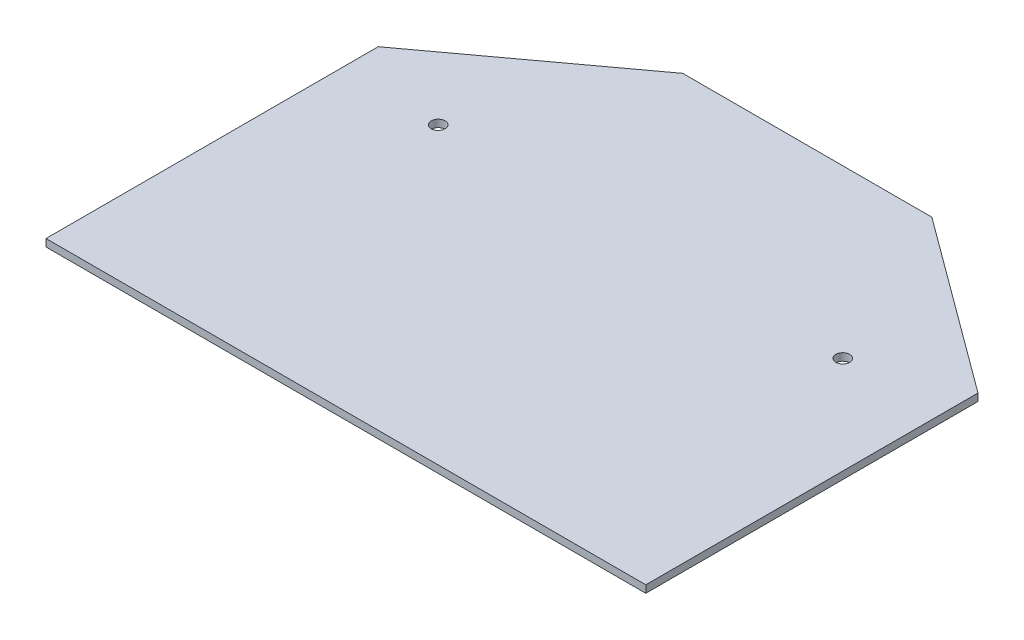
SolidWorks part; units mm, degrees
ref_plane "Front Plane" through (0, 0, 0) normal (0, 0, 1) x (1, 0, 0)
ref_plane "Top Plane" through (0, 0, 0) normal (0, 1, 0) x (1, 0, 0)
ref_plane "Right Plane" through (0, 0, 0) normal (1, 0, 0) x (0, 0, -1)
sketch "Sketch1" plane through (0, 0, 0) normal (0, 1, 0) x (1, 0, 0)
  line L0 (-65, 52) -> (-27, 80)
  line L2 (-65, 52) -> (-65, -20)
  line L3 (-27, 80) -> (0, 80)
  line L4 (0, -20) -> (0, 80)
  line L5 (0, -20) -> (-65, -20)
  line L6 (-59.397, 28.2843) -> (-43.8406, 43.8406) construction
  line L7 (-51.9976, -33.7676) -> (-63.9796, -15.3169) construction
  line L9 (0, 0) -> (-85, 0) construction
  line L10 (-43.8406, 43.8406) -> (0, 0) construction
  line L11 (-51.9976, -33.7676) -> (0, 0) construction
  circle A0 centre (0, 0) radius 85 construction
  circle A1 centre (-43.8406, 43.8406) radius 1.5
  circle A4 centre (-63.9796, -15.3169) radius 1.5 construction
  dimension "D7" = 3
  dimension "D17" = 170
  dimension "D2" = 100
  dimension "D3" = 65
  dimension "D4" = 28
  dimension "D5" = 80
  dimension "D6" = 38
  dimension "D8" = 62
  dimension "D9" = 22
  dimension "D10" = 22
  dimension "D12" = 36.1594
  dimension "D14" = 45
  dimension "D15" = 33
extrude "Boss-Extrude1" add sketch "Sketch1" along normal blind 1.6
mirror "Mirror1" about plane through (0, 1.6, 20) normal (-1, 0, 0) of "Boss-Extrude1"
